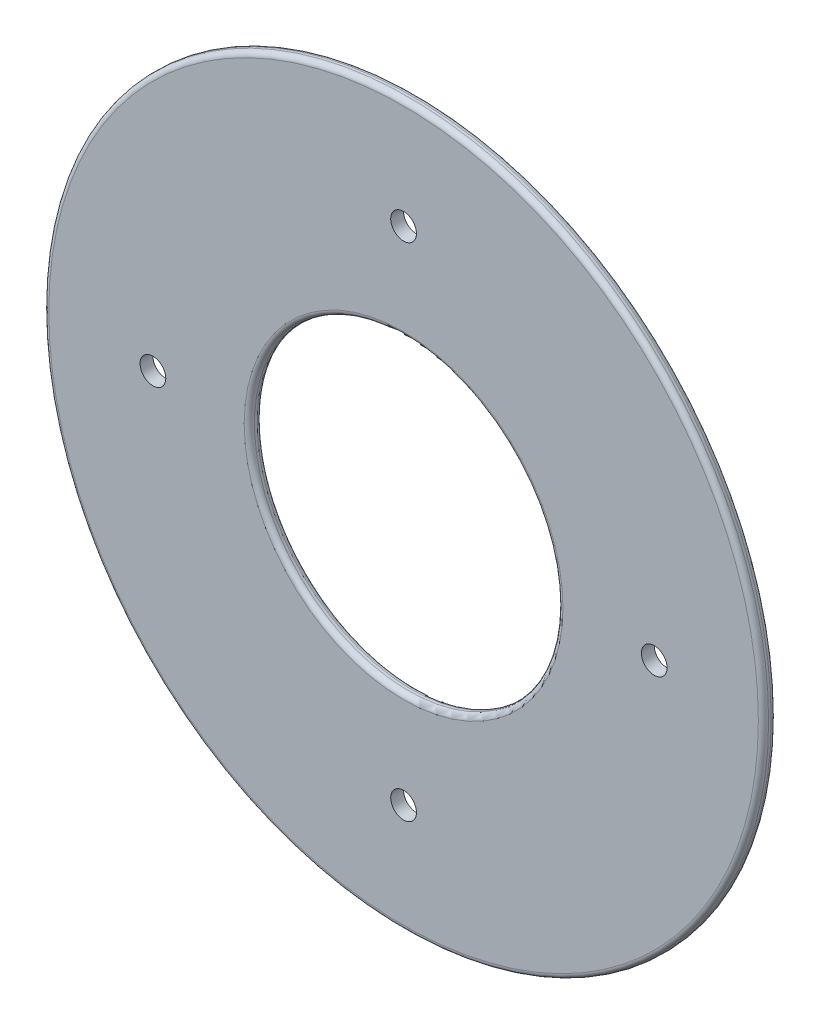
SolidWorks part; units mm, degrees
ref_plane "Front Plane" through (0, 0, 0) normal (0, 0, 1) x (1, 0, 0)
ref_plane "Top Plane" through (0, 0, 0) normal (0, 1, 0) x (1, 0, 0)
ref_plane "Right Plane" through (0, 0, 0) normal (1, 0, 0) x (0, 0, -1)
sketch "Sketch1" plane through (0, 0, 0) normal (0, 0, 1) x (1, 0, 0)
  circle A0 centre (0, 0) radius 88.9
extrude "Boss-Extrude1" add sketch "Sketch1" along normal blind 3.175 contours A0
fillet "Fillet1" radius 1.27 2 edges at (88.9, 0, 0) (88.9, 0, 3.175)
sketch "Sketch2" plane through (0, 0, 3.175) normal (0, 0, 1) x (1, 0, 0)
  circle A0 centre (0, 0) radius 38.1
  circle A1 centre (0, 0) radius 61.9125 construction
  circle A2 centre (0, 61.9125) radius 3.175
  circle A3 centre (61.9125, 0) radius 3.175
  circle A4 centre (0, -61.9125) radius 3.175
  circle A5 centre (-61.9125, 0) radius 3.175
  point P15 (0, 0)
  dimension "D1" = 76.2
  dimension "D2" = 123.825
  dimension "D3" = 4
extrude "Cut-Extrude1" cut sketch "Sketch2" against normal blind 12.7
fillet "Fillet2" radius 1.27 2 edges at (38.1, 0, 0) (38.1, 0, 3.175)
